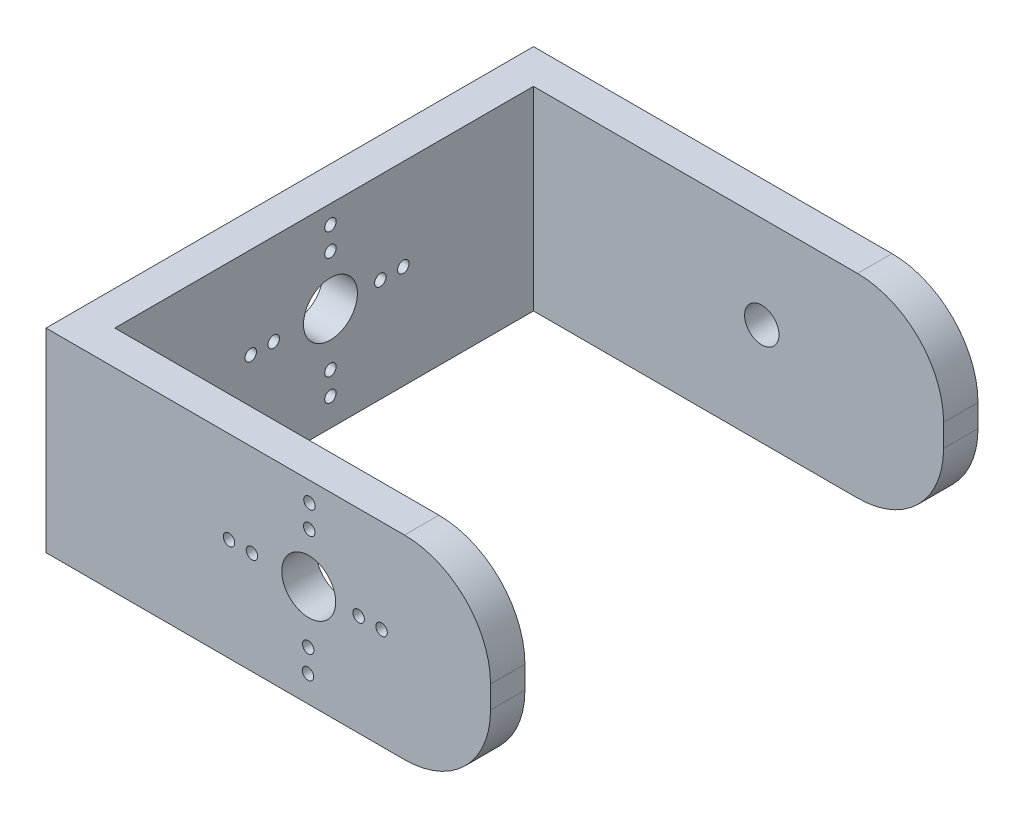
SolidWorks part; units mm, degrees
ref_plane "Front Plane" through (0, 0, 0) normal (0, 0, 1) x (1, 0, 0)
ref_plane "Top Plane" through (0, 0, 0) normal (0, 1, 0) x (1, 0, 0)
ref_plane "Right Plane" through (0, 0, 0) normal (1, 0, 0) x (0, 0, -1)
sketch "Sketch1" plane through (0, 0, 0) normal (0, 0, 1) x (1, 0, 0)
  line L1 (0, 0) -> (-68.3277, 0)
  line L2 (0, 0) -> (0, 52.6864)
  line L3 (0, 52.6864) -> (-68.3277, 52.6864)
  line L4 (-68.3277, 0) -> (-68.3277, 52.6864)
extrude "Boss-Extrude1" add sketch "Sketch1" along normal blind 3
sketch "Sketch2" plane through (0, 0, 0) normal (0, 0, -1) x (-1, 0, 0)
  line L0 (34.7543, 32.2337) -> (0, 32.2337)
  line L1 (68.3277, 0) -> (34.7543, 0)
  line L2 (68.3277, 0) -> (68.3277, 52.6864)
  line L3 (68.3277, 52.6864) -> (34.7543, 52.6864)
  line L4 (34.7543, 15.2724) -> (34.7543, 32.2337)
  line L5 (0, 0) -> (0, 52.6864) construction
  line L6 (34.7543, 15.2724) -> (0, 15.2724)
  line L7 (0, 15.2724) -> (0, 0)
  line L8 (0, 0) -> (34.7543, 0)
  line L9 (0, 52.6864) -> (68.3277, 52.6864) construction
  line L10 (0, 32.2337) -> (0, 52.6864)
  line L11 (0, 52.6864) -> (34.7543, 52.6864)
extrude "Cut-Extrude1" cut sketch "Sketch2" against normal blind 100
sketch "Sketch4" plane through (-34.7543, 0, 0) normal (-1, 0, 0) x (0, 0, 1)
  line L1 (0, 32.2337) -> (3, 32.2337)
  line L2 (0, 32.2337) -> (0, 15.2724)
  line L3 (0, 15.2724) -> (3, 15.2724)
  line L4 (3, 32.2337) -> (3, 15.2724)
extrude "Boss-Extrude2" add sketch "Sketch4" along normal blind 4
sketch "Sketch5" plane through (0, 0, 0) normal (0, 0, -1) x (-1, 0, 0)
  line L0 (38.7543, 15.2724) -> (0, 15.2724) construction
  line L1 (38.7543, 32.2337) -> (35.7543, 32.2337)
  line L2 (38.7543, 32.2337) -> (38.7543, 15.2724)
  line L3 (38.7543, 15.2724) -> (35.7543, 15.2724)
  line L4 (35.7543, 32.2337) -> (35.7543, 15.2724)
  dimension "D1" = 3
extrude "Boss-Extrude3" add sketch "Sketch5" along normal offset from surface (39.5 mm away) 4
sketch "Sketch6" plane through (-35.7543, 0, 0) normal (1, 0, 0) x (0, 0, -1)
  line L0 (39.5, 15.2724) -> (0, 15.2724) construction
  line L1 (39.5, 32.2337) -> (36.5, 32.2337)
  line L2 (39.5, 32.2337) -> (39.5, 15.2724)
  line L3 (39.5, 15.2724) -> (36.5, 15.2724)
  line L4 (36.5, 32.2337) -> (36.5, 15.2724)
  dimension "D1" = 3
extrude "Boss-Extrude4" add sketch "Sketch6" along normal up to surface (35.7543 mm away) up to face at (0, 23.753, 1.5)
fillet "Fillet1" radius 7.5 1 edges at (0, 15.2724, 1.5)
fillet "Fillet2" radius 7.5 1 edges at (0, 32.2337, 1.5)
fillet "Fillet3" radius 7.5 1 edges at (0, 32.2337, -38)
fillet "Fillet4" radius 7.5 1 edges at (0, 15.2724, -38)
sketch "Sketch7" plane through (0, 0, 0) normal (0, 0, -1) x (-1, 0, 0)
  circle A0 centre (15.7855, 30.5158) radius 0.5
  circle A1 centre (15.7855, 30.5158) radius 0.5 construction
  circle A2 centre (15.8056, 28.5159) radius 0.5
  circle A3 centre (15.8056, 28.5159) radius 0.5 construction
  circle A4 centre (20.799, 24.2159) radius 0.5
  circle A5 centre (20.799, 24.2159) radius 0.5 construction
  circle A6 centre (22.7989, 24.236) radius 0.5
  circle A7 centre (22.7989, 24.236) radius 0.5 construction
  circle A8 centre (11.4995, 24.1225) radius 0.5
  circle A9 centre (9.4996, 24.1024) radius 0.5
  circle A10 centre (15.8955, 19.5664) radius 0.5
  circle A11 centre (15.9156, 17.5665) radius 0.5
  circle A12 centre (15.9156, 17.5665) radius 0.5 construction
  circle A13 centre (15.8955, 19.5664) radius 0.5 construction
  circle A14 centre (11.4995, 24.1225) radius 0.5 construction
  circle A15 centre (9.4996, 24.1024) radius 0.5 construction
sketch "Sketch9" plane through (-38.7543, 0, 0) normal (-1, 0, 0) x (0, 0, 1)
  circle A0 centre (-23.1492, 24.2837) radius 0.5
  circle A1 centre (-18.7992, 19.6837) radius 0.5
  circle A2 centre (-13.8492, 24.2837) radius 0.5
  circle A3 centre (-18.7992, 28.6337) radius 0.5
  circle A4 centre (-18.7992, 30.6337) radius 0.5
  circle A5 centre (-18.7992, 17.6837) radius 0.5
  circle A6 centre (-11.8492, 24.2837) radius 0.5
  circle A7 centre (-25.1492, 24.2837) radius 0.5
extrude "Cut-Extrude5" cut sketch "Sketch9" against normal blind 14 contours A2 | A6 | A1 | A5 | A0 | A7 | A4 | A3
extrude "Cut-Extrude6" cut sketch "Sketch7" against normal blind 14
sketch "Sketch10" plane through (-38.7543, 0, 0) normal (-1, 0, 0) x (0, 0, 1)
  circle A0 centre (-18.7992, 24.2837) radius 2.35
  circle A1 centre (-18.7992, 24.2837) radius 2.35 construction
extrude "Cut-Extrude7" cut sketch "Sketch10" against normal blind 10
sketch "Sketch11" plane through (0, 0, 0) normal (0, 0, -1) x (-1, 0, 0)
  circle A0 centre (15.8493, 24.1662) radius 2.35
  circle A1 centre (15.8493, 24.1662) radius 2.35 construction
extrude "Cut-Extrude8" cut sketch "Sketch11" against normal blind 10
sketch "Sketch12" plane through (0, 0, -36.5) normal (0, 0, 1) x (1, 0, 0)
  circle A0 centre (-15.8493, 24.1662) radius 1.5
  circle A1 centre (-15.8493, 24.1662) radius 1.5 construction
extrude "Cut-Extrude9" cut sketch "Sketch12" against normal blind 10
